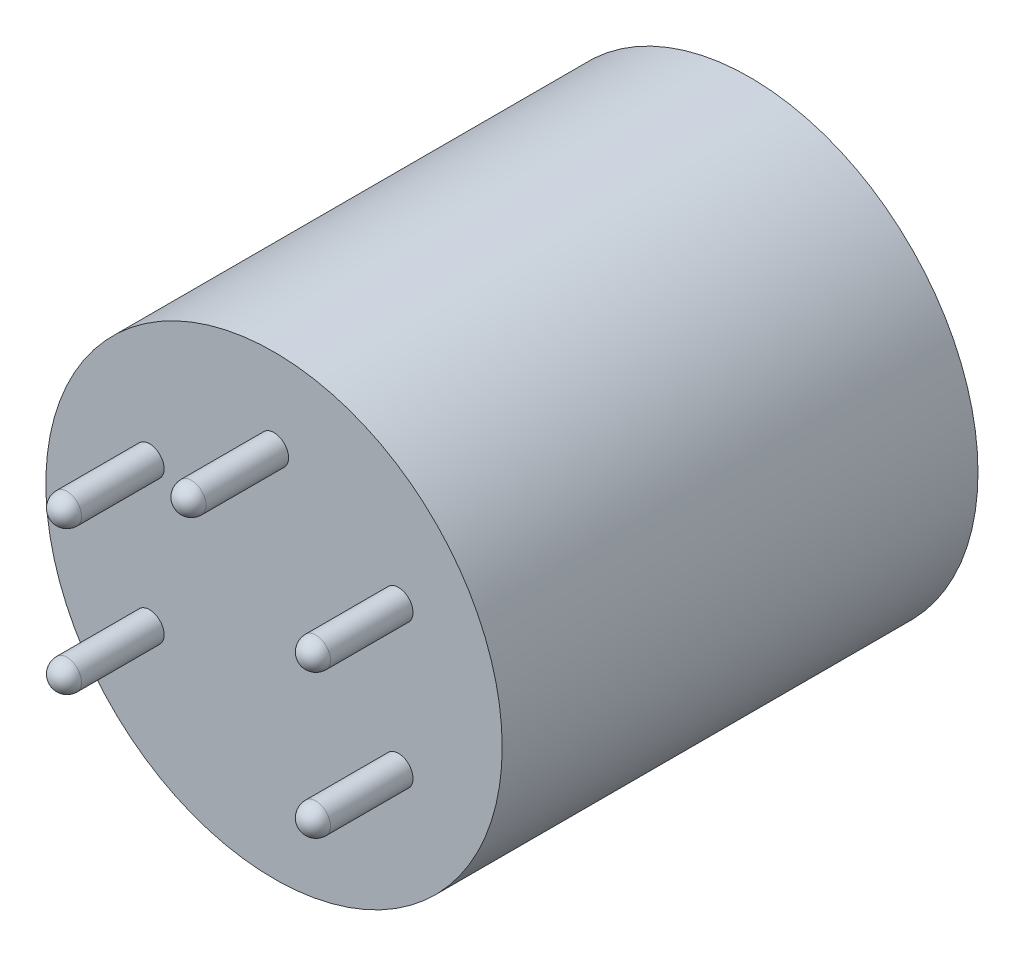
SolidWorks part; units mm, degrees
ref_plane "前视基准面" through (0, 0, 0) normal (0, 0, 1) x (1, 0, 0)
ref_plane "上视基准面" through (0, 0, 0) normal (0, 1, 0) x (1, 0, 0)
ref_plane "右视基准面" through (0, 0, 0) normal (1, 0, 0) x (0, 0, -1)
other "Configuration Table"
sketch "草图1" plane through (0, 0, 0) normal (0, 0, 1) x (1, 0, 0)
  circle A0 centre (0, 0) radius 11.75
  dimension "D1" = 23.5
extrude "凸台-拉伸1" add sketch "草图1" along normal blind 24.5
sketch "草图2" plane through (0, 0, 24.5) normal (0, 0, 1) x (1, 0, 0)
  line L0 (0, 0) -> (0, 7.4) construction
  line L1 (0, 0) -> (-6.4086, 3.7) construction
  line L2 (0, 0) -> (-6.4086, -3.7) construction
  line L3 (0, 0) -> (6.4086, 3.7) construction
  line L4 (0, 0) -> (6.4086, -3.7) construction
  circle A0 centre (0, 0) radius 7.4 construction
  circle A1 centre (-6.4086, 3.7) radius 0.75
  circle A2 centre (0, 7.4) radius 0.75
  circle A3 centre (6.4086, 3.7) radius 0.75
  circle A4 centre (6.4086, -3.7) radius 0.75
  circle A5 centre (-6.4086, -3.7) radius 0.75
  dimension "D1" = 14.8
  dimension "D6" = 1.5
  dimension "D7" = 1.5
  dimension "D8" = 1.5
  dimension "D9" = 1.5
  dimension "D10" = 1.5
  dimension "D2" = 60
  dimension "D3" = 60
  dimension "D4" = 60
  dimension "D5" = 60
extrude "凸台-拉伸2" add sketch "草图2" along normal blind 5
fillet "圆角1" radius 0.75 5 edges at (7.1586, -3.7, 29.5) (7.1586, 3.7, 29.5) (-5.6586, -3.7, 29.5) (0.75, 7.4, 29.5) (-5.6586, 3.7, 29.5)
sketch "草图3" plane through (0, 0, 0) normal (0, 0, -1) x (-1, 0, 0)
  circle A0 centre (0, 0) radius 7.4
  dimension "D1" = 14.8
extrude "切除-拉伸1" cut sketch "草图3" against normal blind 1.5
sketch "草图4" plane through (0, 0, 0) normal (0, 0, -1) x (-1, 0, 0)
  circle A0 centre (0, 0) radius 9.575
  dimension "D1" = 19.15
ref_plane "基准面1" through (0, 0, 0) normal (0, 1, 0) x (1, 0, 0)
sketch "草图5" plane through (0, 0, 0) normal (0, 1, 0) x (1, 0, 0)
  line L0 (11.75, 0) -> (-11.75, 0) construction
  line L1 (9.575, 0) -> (-9.575, 0) construction
  circle A0 centre (-9.575, 0) radius 0.5
  dimension "D1" = 1
sweep "扫描1" add profiles "草图5" path "草图4"
